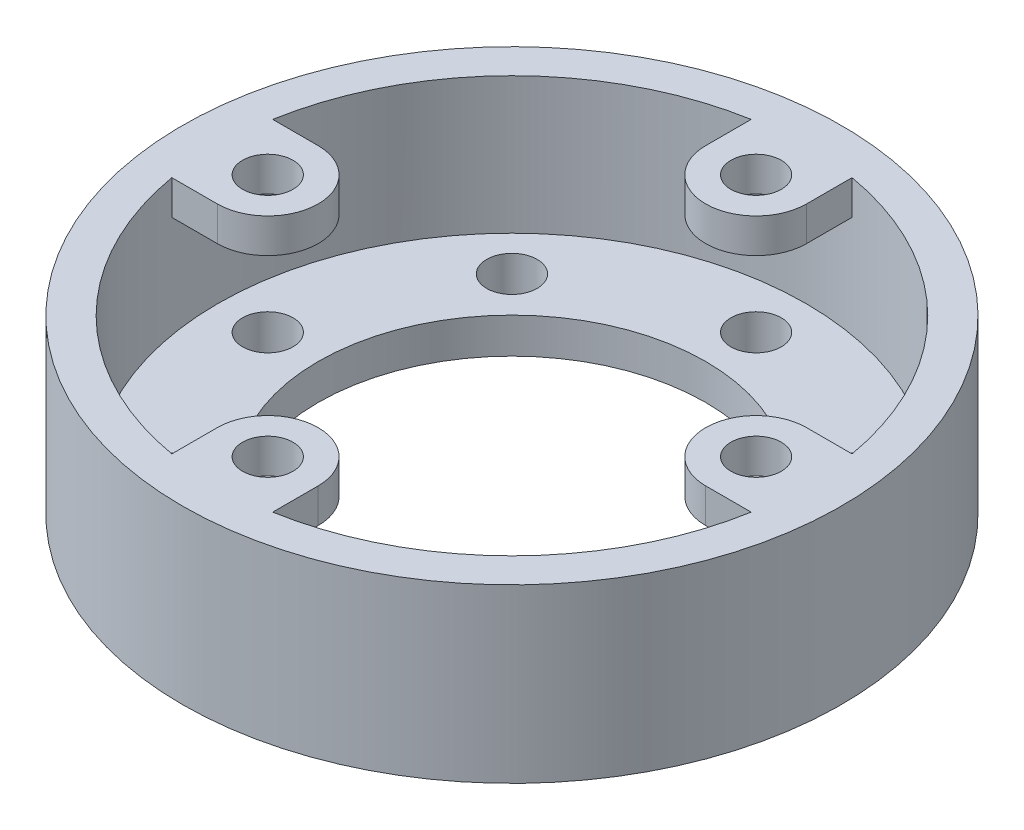
SolidWorks part; units mm, degrees
ref_plane "Front Plane" through (0, 0, 0) normal (0, 0, 1) x (1, 0, 0)
ref_plane "Top Plane" through (0, 0, 0) normal (0, 1, 0) x (1, 0, 0)
ref_plane "Right Plane" through (0, 0, 0) normal (1, 0, 0) x (0, 0, -1)
sketch "Sketch1" plane through (0, 0, 0) normal (0, 0, 1) x (1, 0, 0)
  line L0 (0, 92.8995) -> (0, -126.8465) construction
  line L1 (-65.151, 0) -> (-73.025, 0)
  line L2 (-65.151, 0) -> (-65.151, 38.1)
  line L3 (-65.151, 38.1) -> (-73.025, 38.1)
  line L4 (-73.025, 0) -> (-73.025, 38.1)
  dimension "D1" = 73.025
  dimension "D2" = 38.1
  dimension "D3" = 7.874
revolve "Revolve1" add sketch "Sketch1" angle 360 about L0
sketch "Sketch2" plane through (0, 0, 0) normal (0, 1, 0) x (1, 0, 0)
  circle A0 centre (0, 0) radius 65.151
  circle A1 centre (0, 0) radius 65.151 construction
  circle A2 centre (0, 0) radius 42.926
  dimension "D1" = 85.852
extrude "Boss-Extrude2" add sketch "Sketch2" along normal blind 7.874
sketch "Sketch4" plane through (0, 7.874, 0) normal (0, 1, 0) x (1, 0, 0)
  circle A0 centre (0, 54.102) radius 5.588
  circle A1 centre (0, 0) radius 54.102 construction
  circle A2 centre (38.2559, 38.2559) radius 5.588
  circle A3 centre (54.102, 0) radius 5.588
  circle A4 centre (38.2559, -38.2559) radius 5.588
  circle A5 centre (0, -54.102) radius 5.588
  circle A6 centre (-38.2559, -38.2559) radius 5.588
  circle A7 centre (-54.102, 0) radius 5.588
  circle A8 centre (-38.2559, 38.2559) radius 5.588
  point P23 (0, 0)
  dimension "D1" = 11.176
  dimension "D2" = 108.204
  dimension "D3" = 8
extrude "Cut-Extrude1" cut sketch "Sketch4" against normal through all
sketch "Sketch5" plane through (0, 38.1, 0) normal (0, 1, 0) x (1, 0, 0)
  line L0 (0, 87.3605) -> (0, -30.8597) construction
  line L1 (11.176, 64.1853) -> (11.176, 54.102)
  line L2 (-11.176, 64.1853) -> (-11.176, 54.102)
  line L3 (64.1853, 11.176) -> (54.102, 11.176)
  line L4 (64.1853, -11.176) -> (54.102, -11.176)
  line L5 (11.176, -64.1853) -> (11.176, -54.102)
  line L6 (-11.176, -64.1853) -> (-11.176, -54.102)
  line L7 (-64.1853, -11.176) -> (-54.102, -11.176)
  line L8 (-64.1853, 11.176) -> (-54.102, 11.176)
  circle A0 centre (0, 0) radius 54.102 construction
  circle A1 centre (0, 54.102) radius 5.588
  circle A2 centre (0, 54.102) radius 5.588 construction
  arc A3 (-11.176, 54.102) -> (11.176, 54.102) centre (0, 54.102) ccw
  circle A4 centre (0, 0) radius 65.151 construction
  arc A5 (54.102, 11.176) -> (54.102, -11.176) centre (54.102, 0) ccw
  circle A6 centre (54.102, 0) radius 5.588
  arc A7 (11.176, -54.102) -> (-11.176, -54.102) centre (0, -54.102) ccw
  circle A8 centre (0, -54.102) radius 5.588
  arc A9 (-54.102, -11.176) -> (-54.102, 11.176) centre (-54.102, 0) ccw
  circle A10 centre (-54.102, 0) radius 5.588
  point P37 (0, 0)
  circle M6 centre (0, 0) radius 65.151
  dimension "D1" = 22.352
  dimension "D2" = 4
extrude "Boss-Extrude4" add sketch "Sketch5" against normal blind 7.62 contours L7 A9 L8 A10 M6 | L2 A3 L1 A1 M6 | L3 A5 L4 A6 M6 | L5 A7 L6 A8 M6
